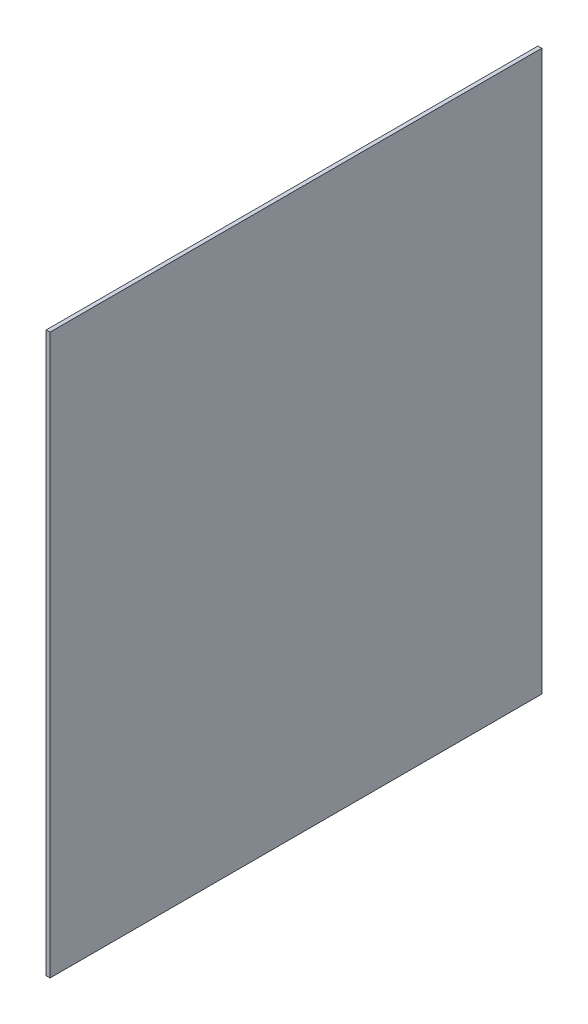
SolidWorks part; units mm, degrees
ref_plane "Front Plane" through (0, 0, 0) normal (0, 0, 1) x (1, 0, 0)
ref_plane "Top Plane" through (0, 0, 0) normal (0, 1, 0) x (1, 0, 0)
ref_plane "Right Plane" through (0, 0, 0) normal (1, 0, 0) x (0, 0, -1)
sketch "Sketch1" plane through (0, 0, 0) normal (1, 0, 0) x (0, 0, -1)
  line L1 (0, 0) -> (203.2, 0)
  line L2 (0, 0) -> (0, 231.14)
  line L3 (0, 231.14) -> (203.2, 231.14)
  line L4 (203.2, 0) -> (203.2, 231.14)
extrude "Boss-Extrude1" add sketch "Sketch1" along normal blind 1.5875
